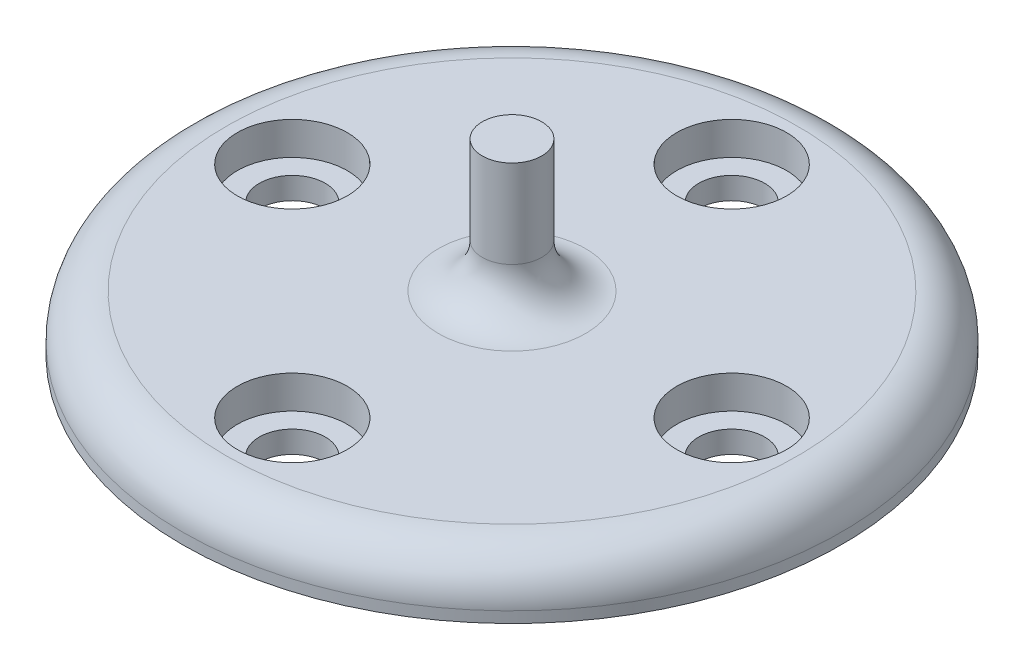
SolidWorks part; units mm, degrees
ref_plane "Front Plane" through (0, 0, 0) normal (0, 0, 1) x (1, 0, 0)
ref_plane "Top Plane" through (0, 0, 0) normal (0, 1, 0) x (1, 0, 0)
ref_plane "Right Plane" through (0, 0, 0) normal (1, 0, 0) x (0, 0, -1)
sketch "Sketch1" plane through (0, 0, 0) normal (0, 1, 0) x (1, 0, 0)
  circle A0 centre (0, 0) radius 15
  dimension "D1" = 30
extrude "Boss-Extrude1" add sketch "Sketch1" along normal blind 2.5
sketch "Sketch2" plane through (0, 2.5, 0) normal (0, 1, 0) x (1, 0, 0)
  circle A0 centre (0, 0) radius 10 construction
  circle A1 centre (0, 10) radius 1.5
  dimension "D1" = 20
  dimension "D2" = 3
extrude "Cut-Extrude1" cut sketch "Sketch2" against normal through all
sketch "Sketch4" plane through (0, 2.5, 0) normal (0, 1, 0) x (1, 0, 0)
  circle A0 centre (0, 10) radius 2.5
  dimension "D1" = 5
extrude "Cut-Extrude2" cut sketch "Sketch4" against normal blind 1.5
pattern_circular "CirPattern1" count 4 over 360 about axis through (0, 0, 0) along (0, 1, 0) of "Cut-Extrude1", "Cut-Extrude2"
sketch "Sketch3" plane through (0, 2.5, 0) normal (0, 1, 0) x (1, 0, 0)
  circle A0 centre (0, 0) radius 1.35
  dimension "D1" = 2.7
extrude "Boss-Extrude2" add sketch "Sketch3" along normal blind 6
fillet "Fillet2" radius 2 1 edges at (0, 2.5, 1.35)
fillet "Fillet3" radius 2 1 edges at (0, 2.5, 15)
